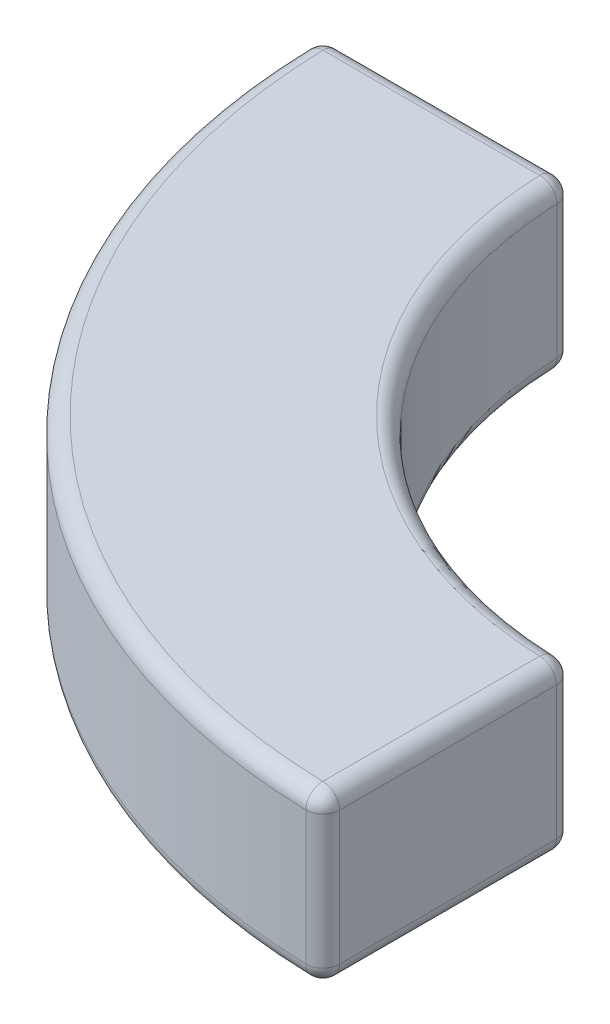
SolidWorks part; units mm, degrees
ref_plane "Front Plane" through (0, 0, 0) normal (0, 0, 1) x (1, 0, 0)
ref_plane "Top Plane" through (0, 0, 0) normal (0, 1, 0) x (1, 0, 0)
ref_plane "Right Plane" through (0, 0, 0) normal (1, 0, 0) x (0, 0, -1)
sketch "Sketch1" plane through (0, 0, 0) normal (0, 1, 0) x (1, 0, 0)
  line L0 (-12.5, 0) -> (-20, 0)
  line L1 (0, -12.5) -> (0, -20)
  line L2 (-12.5, 0) -> (0, 0) construction
  line L3 (0, 0) -> (0, -12.5) construction
  arc A0 (-12.5, 0) -> (0, -12.5) centre (0, 0) ccw
  arc A1 (-20, 0) -> (0, -20) centre (0, 0) ccw
  dimension "D1" = 12.5
  dimension "D2" = 20
extrude "Boss-Extrude1" add sketch "Sketch1" along normal blind 5
fillet "Fillet1" radius 0.5 12 edges at (-12.5, 2.5, 0) (-20, 2.5, 0) (0, 2.5, 20) (0, 2.5, 12.5) (0, 5, 16.25) (-14.1421, 5, 14.1421) (-16.25, 5, 0) (-8.8388, 5, 8.8388) (0, 0, 16.25) (-14.1421, 0, 14.1421) (-16.25, 0, 0) (-8.8388, 0, 8.8388)
